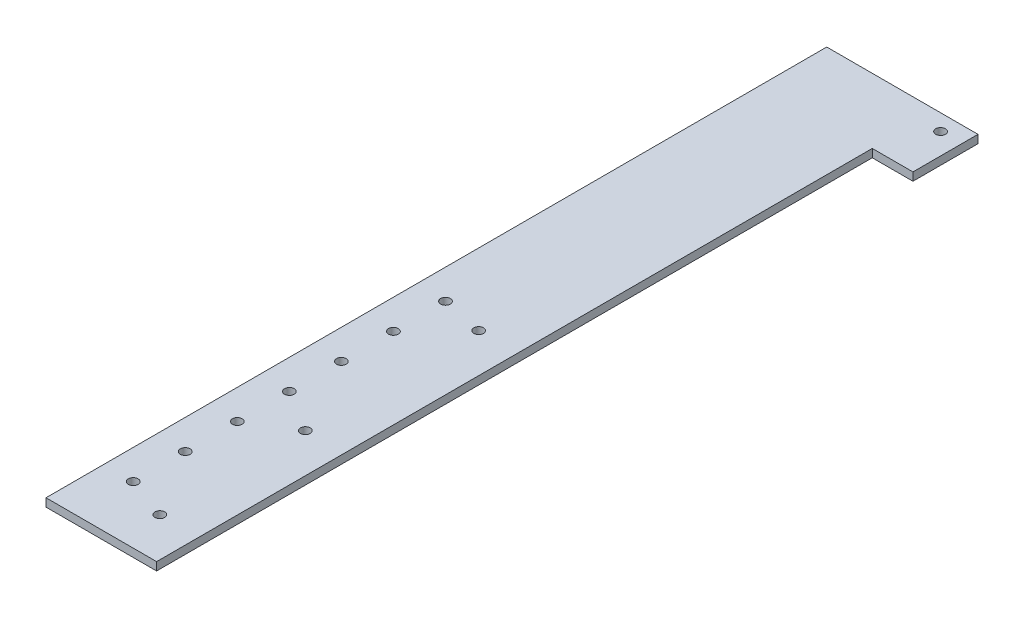
SolidWorks part; units mm, degrees
ref_plane "Front Plane" through (0, 0, 0) normal (0, 0, 1) x (1, 0, 0)
ref_plane "Top Plane" through (0, 0, 0) normal (0, 1, 0) x (1, 0, 0)
ref_plane "Right Plane" through (0, 0, 0) normal (1, 0, 0) x (0, 0, -1)
sketch "Sketch1" plane through (0, 0, 0) normal (0, 1, 0) x (1, 0, 0)
  line L1 (0, 0) -> (25.4, 0)
  line L2 (0, 0) -> (0, 304.8)
  line L3 (0, 304.8) -> (25.4, 304.8)
  line L4 (25.4, 0) -> (25.4, 304.8)
  line L5 (0, 304.8) -> (41.275, 304.8)
  line L6 (0, 304.8) -> (0, 279.4)
  line L7 (0, 279.4) -> (41.275, 279.4)
  line L8 (41.275, 304.8) -> (41.275, 279.4)
  dimension "D1" = 304.8
  dimension "D2" = 25.4
  dimension "D3" = 41.275
  dimension "D4" = 25.4
extrude "Boss-Extrude1" add sketch "Sketch1" along normal blind 3.175 contours L2 L7 L4 L3 | L8 L5 L4 L7 | L7 L2 L1 L4
hole_wizard "#25 (0.1495) Diameter Hole2" positions "Sketch2" profile "Sketch3" hole size "#25" standard "ANSI Inch" end condition through all
sketch "Sketch2" plane through (0, 3.175, 0) normal (0, 1, 0) x (1, 0, 0)
  line L0 (10.16, -11.2576) -> (10.16, 313.3267) construction
  line L1 (0, 0) -> (25.4, 0) construction
  line L4 (0, 0) -> (0, 304.8) construction
  point P0 (10.16, 16.51)
  point P2 (10.16, 73.3083)
  point P4 (10.16, 140.97)
  point P7 (33.02, 298.45)
  dimension "D1" = 10.16
  dimension "D2" = 22.86
  dimension "D3" = 16.51
  dimension "D4" = 56.7983
  dimension "D5" = 124.46
  dimension "D6" = 157.48
sketch "Sketch3" plane through (10.16, 3.175, -16.51) normal (1, 0, 0) x (0, 0, 1)
  line L0 (0, 0) -> (0, 3.175)
  line L1 (0, 3.175) -> (1.8986, 3.175)
  line L2 (1.8986, 3.175) -> (1.8986, 0)
  line L5 (1.8986, 0) -> (0, 0)
  line L11 (0, -6.35) -> (0, 107.95) construction
  dimension "Thru Hole Dia." = 3.7973
  dimension "Thru Hole Depth" = 3.175
sketch "Sketch4" plane through (0, 0, 0) normal (-1, 0, 0) x (0, 0, 1)
  line L4 (-304.8, 0) -> (0, 0)
  line L5 (0, 0) -> (0, 3.175)
  line L6 (0, 3.175) -> (-304.8, 3.175)
  line L7 (-304.8, 3.175) -> (-304.8, 0)
  line L8 (-304.8, 0) -> (0, 0)
  line L9 (0, 0) -> (0, 3.175)
  line L10 (0, 3.175) -> (-304.8, 3.175)
  line L11 (-304.8, 3.175) -> (-304.8, 0)
  dimension "D1" = 0
extrude "Boss-Extrude2" add sketch "Sketch4" along normal blind 17.78
sketch "Sketch5" plane through (0, 3.175, 0) normal (0, 1, 0) x (1, 0, 0)
  line L0 (-6.223, 0) -> (-6.223, 304.8) construction
  line L3 (-17.78, 0) -> (25.4, 0) construction
  line L4 (-17.78, 304.8) -> (41.275, 304.8) construction
  line L5 (0, 0) -> (0, 304.8) construction
  line L6 (0, 304.8) -> (243.84, 304.8) construction
  line L7 (243.84, 304.8) -> (243.84, 0) construction
  line L8 (243.84, 0) -> (0, 0) construction
  line L9 (-6.223, 22.479) -> (-6.223, 42.799) construction
  circle A2 centre (-6.223, 42.799) radius 0.127
  circle A3 centre (-6.223, 22.479) radius 0.127
  circle A4 centre (-6.223, 63.119) radius 0.127
  circle A5 centre (-6.223, 83.439) radius 0.127
  circle A6 centre (-6.223, 103.759) radius 0.127
  circle A7 centre (-6.223, 124.079) radius 0.127
  circle A8 centre (-6.223, 144.399) radius 0.127
  dimension "D4" = 7
  dimension "D3" = 22.479
  dimension "D6" = 0.254
  dimension "D1" = 243.84
  dimension "D2" = 6.223
  dimension "D5" = 20.32
extrude "Cut-Extrude1" cut sketch "Sketch5" against normal through all
hole_wizard "#25 (0.1495) Diameter Hole1" positions "Sketch6" profile "Sketch7" hole size "#25" standard "ANSI Inch" end condition through all
sketch "Sketch6" plane through (0, 3.175, 0) normal (0, 1, 0) x (1, 0, 0)
  circle A1 centre (-6.223, 144.399) radius 0.127 construction
  circle A2 centre (-6.223, 124.079) radius 0.127 construction
  circle A3 centre (-6.223, 103.759) radius 0.127 construction
  circle A4 centre (-6.223, 83.439) radius 0.127 construction
  circle A5 centre (-6.223, 63.119) radius 0.127 construction
  circle A6 centre (-6.223, 42.799) radius 0.127 construction
  circle A7 centre (-6.223, 22.479) radius 0.127 construction
  point P4 (-6.223, 42.799)
  point P6 (-6.223, 63.119)
  point P8 (-6.223, 83.439)
  point P10 (-6.223, 103.759)
  point P12 (-6.223, 124.079)
  point P14 (-6.223, 144.399)
  point P33 (-6.223, 22.479)
sketch "Sketch7" plane through (-6.223, 3.175, -42.799) normal (1, 0, 0) x (0, 0, 1)
  line L0 (0, 0) -> (0, 3.175)
  line L1 (0, 3.175) -> (1.8986, 3.175)
  line L2 (1.8986, 3.175) -> (1.8986, 0)
  line L5 (1.8986, 0) -> (0, 0)
  line L11 (0, -6.35) -> (0, 107.95) construction
  dimension "Thru Hole Dia." = 3.7973
  dimension "Thru Hole Depth" = 3.175
